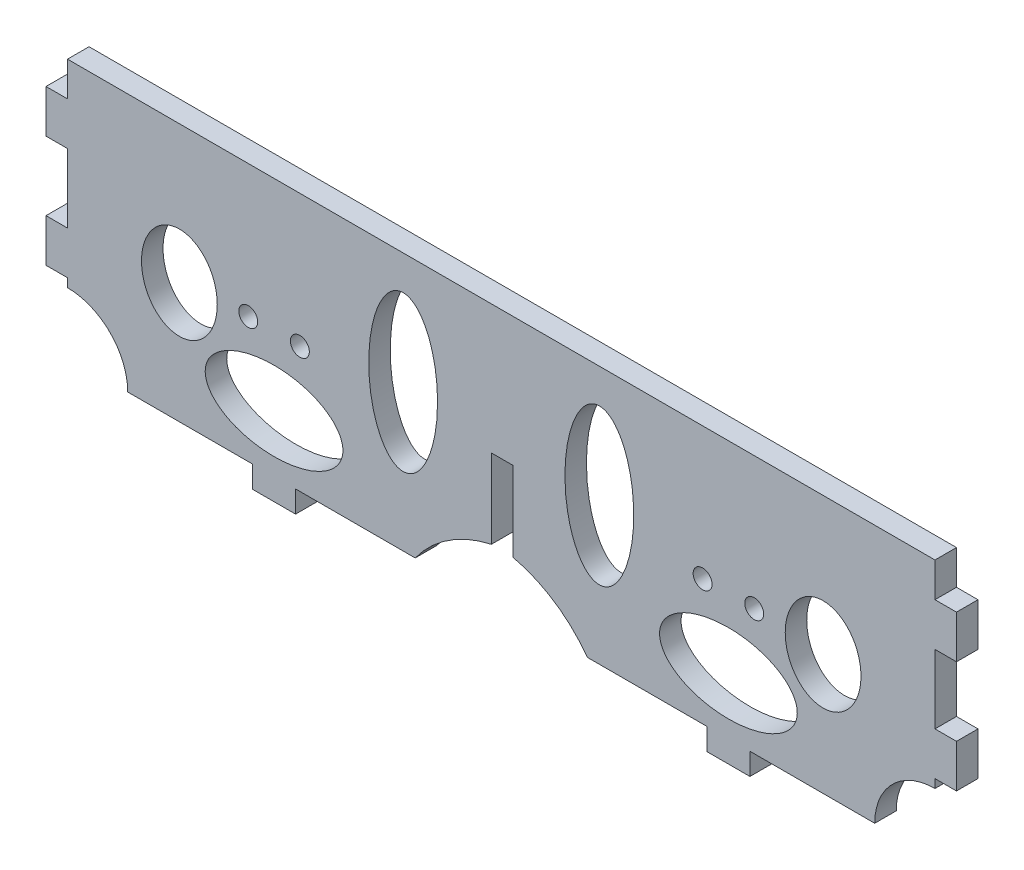
SolidWorks part; units mm, degrees
ref_plane "Front Plane" through (0, 0, 0) normal (0, 0, 1) x (1, 0, 0)
ref_plane "Top Plane" through (0, 0, 0) normal (0, 1, 0) x (1, 0, 0)
ref_plane "Right Plane" through (0, 0, 0) normal (1, 0, 0) x (0, 0, -1)
sketch "Sketch1" plane through (0, 0, 0) normal (0, 0, 1) x (1, 0, 0)
  line L1 (-64.008, -19.05) -> (64.008, -19.05)
  line L2 (-64.008, -19.05) -> (-64.008, 19.05)
  line L3 (-64.008, 19.05) -> (64.008, 19.05)
  line L4 (64.008, -19.05) -> (64.008, 19.05)
  line L5 (-64.008, -19.05) -> (64.008, 19.05) construction
  line L6 (-64.008, 19.05) -> (64.008, -19.05) construction
  point P0 (0, 0)
  dimension "D1" = 38.1
  dimension "D2" = 128.016
extrude "main body" add sketch "Sketch1" along normal blind 3.175
sketch "Sketch2" plane through (0, 0, 3.175) normal (0, 0, 1) x (1, 0, 0)
  line L0 (-37.338, -0.508) -> (-29.718, -0.508) construction
  line L1 (-33.528, -0.508) -> (-33.528, -1.6634) construction
  line L2 (0, 19.05) -> (0, -19.05) construction
  line L3 (64.008, 19.05) -> (-64.008, 19.05) construction
  line L4 (-64.008, -19.05) -> (64.008, -19.05) construction
  circle A0 centre (-29.718, -0.508) radius 1.397
  circle A1 centre (-37.338, -0.508) radius 1.397
  dimension "D1" = 2.794
  dimension "D2" = 2.794
  dimension "D3" = 3.81
  dimension "D4" = 33.528
  dimension "D5" = 18.542
extrude "ubracket holes" cut sketch "Sketch2" against normal through all
sketch "Sketch3" plane through (0, 0, 3.175) normal (0, 0, 1) x (1, 0, 0)
  line L0 (-64.008, 13.97) -> (-67.183, 13.97)
  line L1 (-64.008, 19.05) -> (-64.008, -19.05) construction
  line L2 (-67.183, 13.97) -> (-67.183, 7.62)
  line L3 (-67.183, 7.62) -> (-64.008, 7.62)
  line L4 (-64.008, 7.62) -> (-64.008, 13.97)
  line L5 (-64.008, -2.54) -> (-67.183, -2.54)
  line L6 (-67.183, -2.54) -> (-67.183, -8.89)
  line L7 (-67.183, -8.89) -> (-64.008, -8.89)
  line L8 (-64.008, -8.89) -> (-64.008, -2.54)
  line L10 (-37.338, -0.508) -> (-29.718, -0.508) construction
  line L11 (-33.528, -0.508) -> (-33.528, -38.9824) construction
  line L12 (-33.528, -19.05) -> (-30.353, -19.05)
  line L13 (-64.008, -19.05) -> (64.008, -19.05) construction
  line L14 (-30.353, -19.05) -> (-30.353, -22.2758)
  line L15 (-30.353, -22.2758) -> (-36.703, -22.2758)
  line L16 (-36.703, -22.2758) -> (-36.703, -19.05)
  line L17 (-36.703, -19.05) -> (-33.528, -19.05)
  line L18 (-64.008, 0) -> (0, 0) construction
  dimension "D1" = 6.35
  dimension "D2" = 3.175
  dimension "D3" = 3.175
  dimension "D4" = 6.35
  dimension "D5" = 7.62
  dimension "D6" = 2.54
  dimension "D7" = 3.175
  dimension "D8" = 6.35
  dimension "D9" = 3.2258
  dimension "D10" = 10.16
extrude "tabs" add sketch "Sketch3" against normal blind 3.175
sketch "Sketch4" plane through (0, 0, 3.175) normal (0, 0, 1) x (1, 0, 0)
  line L0 (-30.353, -19.05) -> (64.008, -19.05) construction
  line L1 (0, 19.05) -> (0, -19.05) construction
  line L2 (64.008, 19.05) -> (-64.008, 19.05) construction
  line L3 (-37.338, -0.508) -> (-29.718, -0.508) construction
  line L4 (-33.528, -0.508) -> (-33.528, -1.5813) construction
  line L6 (-64.008, -19.05) -> (-36.703, -19.05) construction
  ellipse E0 centre (-14.478, 2.54) end of major axis (-14.478, 13.97) minor radius 5.08
  ellipse E1 centre (-33.5275, -10.668) end of major axis (-23.3675, -10.668) minor radius 5.842
  ellipse E2 centre (-47.498, -1.27) end of major axis (-47.498, 5.588) minor radius 5.588
  dimension "D1" = 11.43
  dimension "D2" = 5.08
  dimension "D3" = 21.59
  dimension "D4" = 19.05
  dimension "D5" = 5.842
  dimension "D6" = 10.16
  dimension "D7" = 10.16
  dimension "D8" = 6.858
  dimension "D9" = 5.588
  dimension "D10" = 17.78
  dimension "D11" = 13.97
extrude "holes for control arms" cut sketch "Sketch4" against normal through all
mirror "mirror of ubracket holes" about plane through (0, 0, 0) normal (1, 0, 0) of "ubracket holes"
mirror "mirror of tabs" about plane through (0, 0, 0) normal (1, 0, 0) of "tabs"
mirror "Mirror3" about plane through (0, 0, 0) normal (1, 0, 0) of "holes for control arms"
sketch "Sketch5" plane through (0, 0, 3.175) normal (0, 0, 1) x (1, 0, 0)
  line L0 (-30.353, -19.05) -> (30.353, -19.05) construction
  line L3 (-1.4569, 0) -> (1.7181, 0)
  line L4 (-1.4569, 0) -> (-1.4569, -19.05)
  line L5 (-1.4569, -19.05) -> (1.7181, -19.05)
  line L6 (1.7181, 0) -> (1.7181, -19.05)
  line L7 (-1.4569, 0) -> (1.7181, -19.05) construction
  line L8 (-1.4569, -19.05) -> (1.7181, 0) construction
  point P0 (0.1306, -9.525)
  dimension "D1" = 19.05
  dimension "D2" = 3.175
extrude "slot for nose panel" cut sketch "Sketch5" against normal through all
sketch "Sketch6" plane through (0, 0, 3.175) normal (0, 0, 1) x (1, 0, 0)
  line L0 (0, 0) -> (0, -19.05) construction
  line L2 (0, -19.05) -> (0, -11.43)
  line L4 (-30.353, -19.05) -> (-1.4569, -19.05) construction
  line L5 (-64.008, -19.05) -> (-55.118, -19.05)
  line L6 (-64.008, -19.05) -> (-36.703, -19.05) construction
  line L7 (-64.008, -19.05) -> (-64.008, -10.16)
  line L8 (-64.008, -8.89) -> (-64.008, -19.05) construction
  line L9 (-12.7, -19.05) -> (0, -19.05)
  arc A0 (-55.118, -19.05) -> (-64.008, -10.16) centre (-64.008, -19.05) ccw
  arc A1 (-12.7, -19.05) -> (0, -11.43) centre (2.4917, -29.9761) cw
  dimension "D1" = 12.7
  dimension "D2" = 7.62
  dimension "D3" = 8.89
  dimension "D4" = 8.89
extrude "cut corner for screw access" cut sketch "Sketch6" against normal through all
mirror "Mirror4" about plane through (0, 0, 0) normal (1, 0, 0) of "cut corner for screw access"
